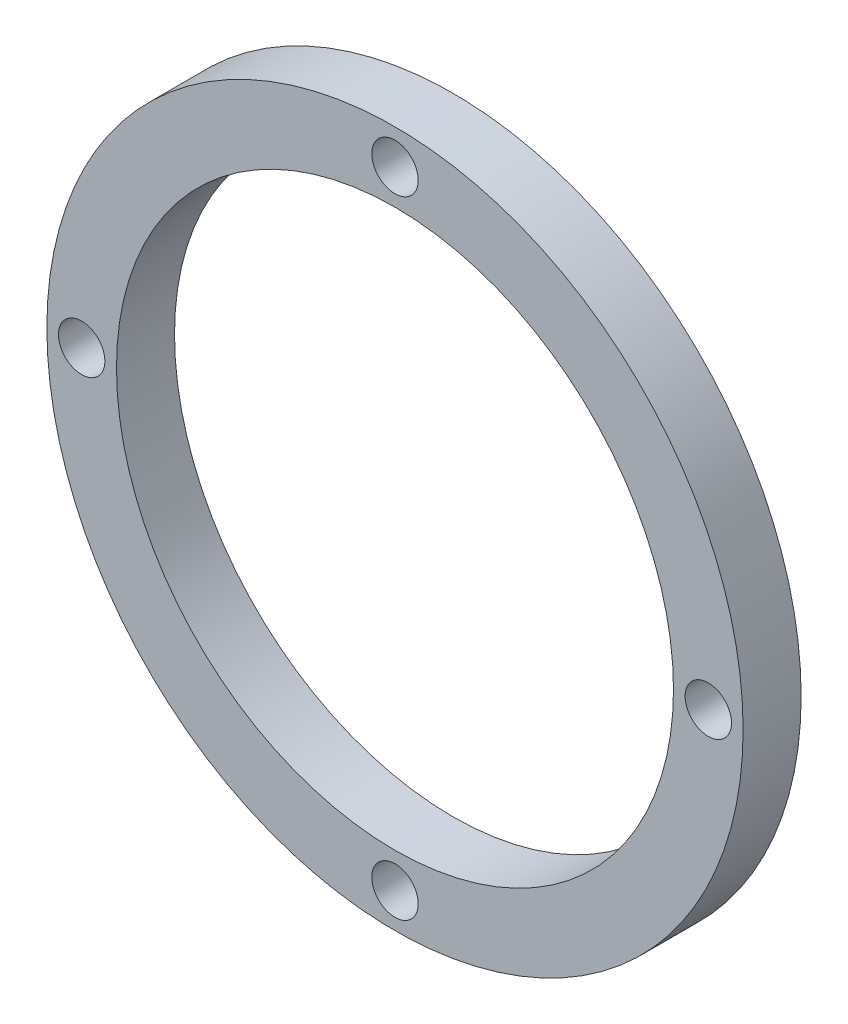
SolidWorks part; units mm, degrees
ref_plane "Front" through (0, 0, 0) normal (0, 0, 1) x (1, 0, 0)
ref_plane "Top" through (0, 0, 0) normal (0, 1, 0) x (1, 0, 0)
ref_plane "Right" through (0, 0, 0) normal (1, 0, 0) x (0, 0, -1)
sketch "Sketch1" plane through (0, 0, 0) normal (0, 0, 1) x (1, 0, 0)
  circle A0 centre (0, 0) radius 12
  circle A1 centre (0, 0) radius 15
  circle A3 centre (0, 13.5) radius 1
  circle A4 centre (13.5, 0) radius 1
  circle A5 centre (0, -13.5) radius 1
  circle A6 centre (-13.5, 0) radius 1
  dimension "D1" = 4
extrude "Boss-Extrude1" add sketch "Sketch1" along normal blind 1
sketch "Sketch2" plane through (0, 0, 1) normal (0, 0, 1) x (1, 0, 0)
  circle A0 centre (0, 0) radius 12
  circle A1 centre (0, 13.5) radius 1
  circle A2 centre (13.5, 0) radius 1
  circle A3 centre (0, -13.5) radius 1
  circle A4 centre (-13.5, 0) radius 1
  circle A5 centre (0, 0) radius 15
  dimension "D1" = 4
extrude "Boss-Extrude3" add sketch "Sketch2" along normal blind 1.5
